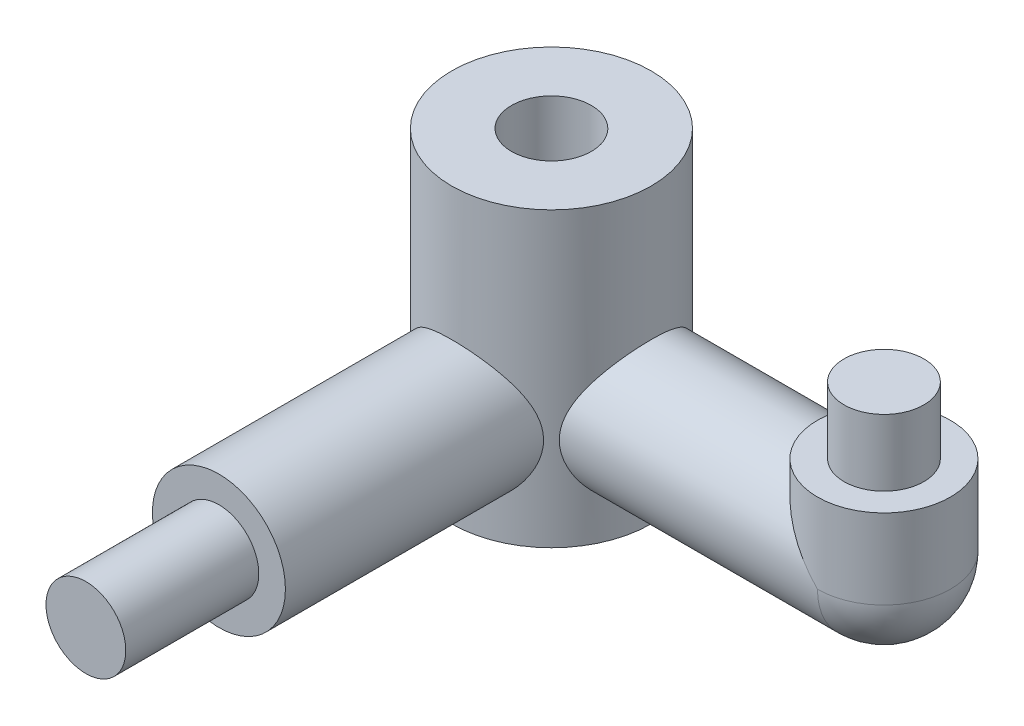
SolidWorks part; units mm, degrees
ref_plane "Front Plane" through (0, 0, 0) normal (0, 0, 1) x (1, 0, 0)
ref_plane "Top Plane" through (0, 0, 0) normal (0, 1, 0) x (1, 0, 0)
ref_plane "Right Plane" through (0, 0, 0) normal (1, 0, 0) x (0, 0, -1)
sketch "Sketch1" plane through (0, 0, 0) normal (0, 0, 1) x (1, 0, 0)
  circle A0 centre (0, 0) radius 2.5
  dimension "D1" = 5
extrude "Boss-Extrude1" add sketch "Sketch1" along normal blind 12.5
sketch "Sketch2" plane through (0, 0, 0) normal (0, 0, -1) x (-1, 0, 0)
  circle A0 centre (0, 0) radius 1.5
  dimension "D1" = 3
extrude "Boss-Extrude2" add sketch "Sketch2" along normal blind 5
sketch "Sketch4" plane through (0, 0, 0) normal (1, 0, 0) x (0, 0, -1)
  line L0 (-12.5, 2.5) -> (-12.5, -2.5) construction
  circle A0 centre (-12.5, 0) radius 2.5
extrude "Boss-Extrude3" add sketch "Sketch4" along normal blind 12.5
sketch "Sketch5" plane through (0, 0, 0) normal (0, 1, 0) x (1, 0, 0)
  line L0 (12.5, -15) -> (12.5, -10) construction
  circle A0 centre (12.5, -12.5) radius 2.5
extrude "Boss-Extrude4" add sketch "Sketch5" along normal blind 3
sketch "Sketch6" plane through (0, 3, 0) normal (0, 1, 0) x (1, 0, 0)
  circle A0 centre (12.5, -12.5) radius 1.5
  dimension "D1" = 3
extrude "Boss-Extrude5" add sketch "Sketch6" along normal blind 2.5
sketch "Sketch8" plane through (0, 0, 0) normal (-1, 0, 0) x (0, 0, 1)
  line L2 (12.5, 2.5) -> (12.5, -2.5)
  line L3 (12.5, 2.5) -> (12.5, -2.5)
  arc A2 (12.5, -2.5) -> (12.5, 2.5) centre (12.5, 0) ccw
  arc A3 (12.5, -2.5) -> (12.5, 2.5) centre (12.5, 0) ccw
  dimension "D1" = 0
revolve "Revolve2" add sketch "Sketch8" angle 90 about L3
sketch "Sketch16" plane through (0, 0, 0) normal (0, -1, 0) x (1, 0, 0)
  line L2 (12.5, 15) -> (12.5, 10)
  line L3 (12.5, 15) -> (12.5, 10)
  arc A2 (12.5, 10) -> (12.5, 15) centre (12.5, 12.5) ccw
  arc A3 (12.5, 10) -> (12.5, 15) centre (12.5, 12.5) ccw
  dimension "D1" = 0
revolve "Revolve3" add sketch "Sketch16" angle 90 about L3
sketch "Sketch18" plane through (0, 0, 0) normal (0, 1, 0) x (1, 0, 0)
  line L0 (0, -12.5) -> (2.5, -10) construction
  circle A0 centre (0, -12.5) radius 3.75
  dimension "D1" = 7.5
extrude "Boss-Extrude6" add sketch "Sketch18" along normal blind 7.5 and the other way blind 3.5
ref_plane "Plane1" through (0, 0, 12.5) normal (0, 0, 1) x (1, 0, 0)
mirror "Mirror1" about plane through (0, 0, 12.5) normal (0, 0, 1) of "Boss-Extrude2", "Boss-Extrude1"
sketch "Sketch20" plane through (0, 7.5, 0) normal (0, 1, 0) x (1, 0, 0)
  circle A0 centre (0, -12.5) radius 1.5
  dimension "D1" = 3
extrude "Cut-Extrude2" cut sketch "Sketch20" against normal through all both and the other way through all
sketch "Sketch21" plane through (0, 7.5, 0) normal (0, 1, 0) x (1, 0, 0)
  line L0 (0, -12.5) -> (0, -8.75) construction
  line L1 (2.6533, -9.85) -> (12.2819, 10.075)
  line L2 (12.2819, 10.075) -> (-12.7946, 9.4363)
  line L3 (-12.7946, 9.4363) -> (-2.6533, -9.85)
  circle A2 centre (0, -12.5) radius 3.75
  arc A3 (2.6533, -9.85) -> (-2.6533, -9.85) centre (0, -12.5) ccw
  point P0 (2.6533, -9.85)
  point P3 (-2.6533, -9.85)
  dimension "D2" = 2.65
  dimension "D1" = 0
extrude "Cut-Extrude3" cut sketch "Sketch21" against normal through all both and the other way through all
